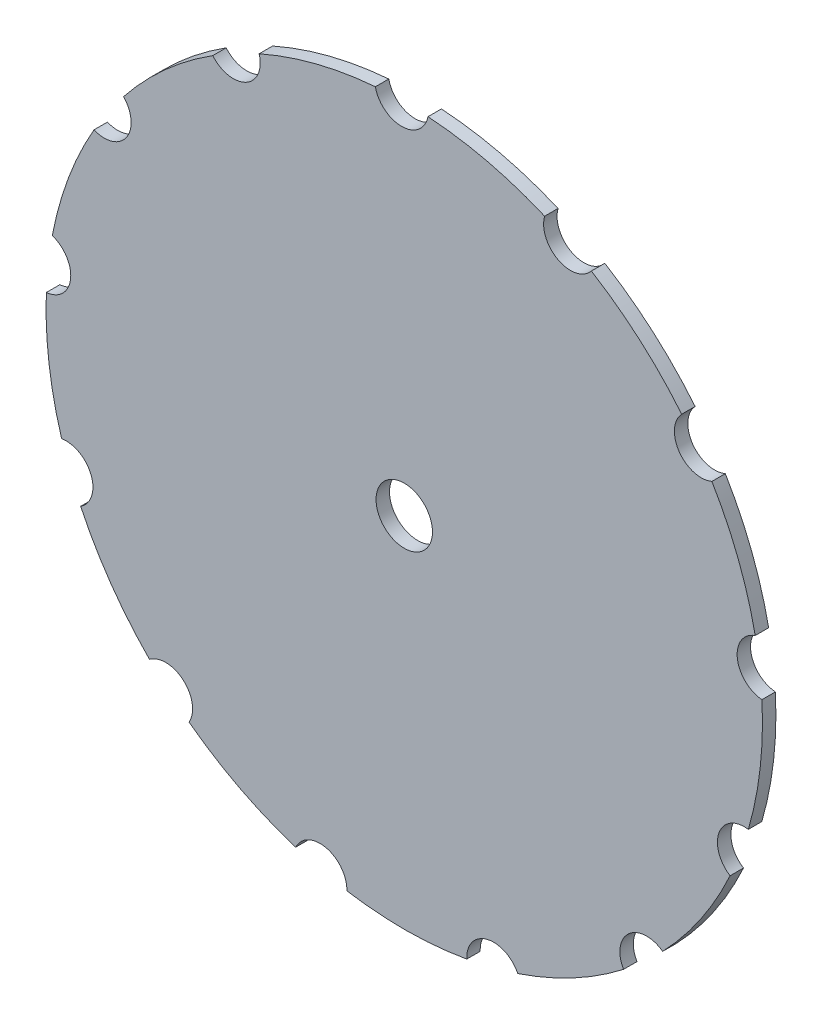
SolidWorks part; units mm, degrees
material "1.0038 (S235JRG2)"
ref_plane "Plan de face" through (0, 0, 0) normal (0, 0, 1) x (1, 0, 0)
ref_plane "Plan de dessus" through (0, 0, 0) normal (0, 1, 0) x (1, 0, 0)
ref_plane "Plan de droite" through (0, 0, 0) normal (1, 0, 0) x (0, 0, -1)
sketch "Esquisse1" plane through (0, 0, 0) normal (0, 0, 1) x (1, 0, 0)
  arc A0 (-85.5426, 135.2127) -> (-125.3707, 99.4092) centre (0, 0) ccw
  circle A1 centre (0, 0) radius 12.6
  arc A2 (-85.5426, 135.2127) -> (-64.8124, 146.2852) centre (-76.3234, 142.8942) ccw
  arc A3 (-12.9078, 159.4785) -> (10.5935, 159.6489) centre (-1.1747, 161.9957) ccw
  arc A4 (62.6841, 147.2097) -> (83.5727, 136.439) centre (74.243, 143.986) ccw
  arc A5 (123.9158, 101.217) -> (137.4063, 81.9726) centre (132.6525, 92.9909) ccw
  arc A6 (156.7599, 32.0366) -> (159.7618, 8.7273) centre (160.673, 20.6926) ccw
  arc A7 (153.6921, -44.4829) -> (145.5178, -66.5174) centre (151.8852, -56.3461) ccw
  arc A8 (115.4154, -110.8119) -> (97.9374, -126.5237) centre (108.3024, -120.4766) ccw
  arc A9 (50.6984, -151.7553) -> (27.9208, -157.545) centre (39.9087, -157.0073) ccw
  arc A10 (-25.633, -157.9334) -> (-48.4922, -152.4746) centre (-37.6275, -157.5696) ccw
  arc A11 (-96.0922, -127.9308) -> (-113.7962, -112.4741) centre (-106.5437, -122.0346) ccw
  arc A12 (-144.5378, -68.6208) -> (-153.0309, -46.7072) centre (-151.0521, -58.5429) ccw
  arc A13 (-159.8716, 6.4094) -> (-157.208, 29.7598) centre (-160.9562, 18.3602) ccw
  arc A14 (-138.5807, 79.9712) -> (-125.3707, 99.4092) centre (-133.9872, 91.0573) ccw
  arc A15 (-12.9078, 159.4785) -> (-64.8124, 146.2852) centre (0, 0) ccw
  arc A16 (62.6841, 147.2097) -> (10.5935, 159.6489) centre (0, 0) ccw
  arc A17 (123.9158, 101.217) -> (83.5727, 136.439) centre (0, 0) ccw
  arc A18 (156.7599, 32.0366) -> (137.4063, 81.9726) centre (0, 0) ccw
  arc A19 (153.6921, -44.4829) -> (159.7618, 8.7273) centre (0, 0) ccw
  arc A20 (115.4154, -110.8119) -> (145.5178, -66.5174) centre (0, 0) ccw
  arc A21 (50.6984, -151.7553) -> (97.9374, -126.5237) centre (0, 0) ccw
  arc A22 (-25.633, -157.9334) -> (27.9208, -157.545) centre (0, 0) ccw
  arc A23 (-96.0922, -127.9308) -> (-48.4922, -152.4746) centre (0, 0) ccw
  arc A24 (-144.5378, -68.6208) -> (-113.7962, -112.4741) centre (0, 0) ccw
  arc A25 (-159.8716, 6.4094) -> (-153.0309, -46.7072) centre (0, 0) ccw
  arc A26 (-138.5807, 79.9712) -> (-157.208, 29.7598) centre (0, 0) ccw
  point P33 (0, 0)
  dimension "D1" = 25.2
  dimension "D2" = 320
  dimension "D3" = 24
  dimension "D4" = 162
  dimension "D5" = 13
extrude "Boss.-Extru.1" add sketch "Esquisse1" along normal blind 6
